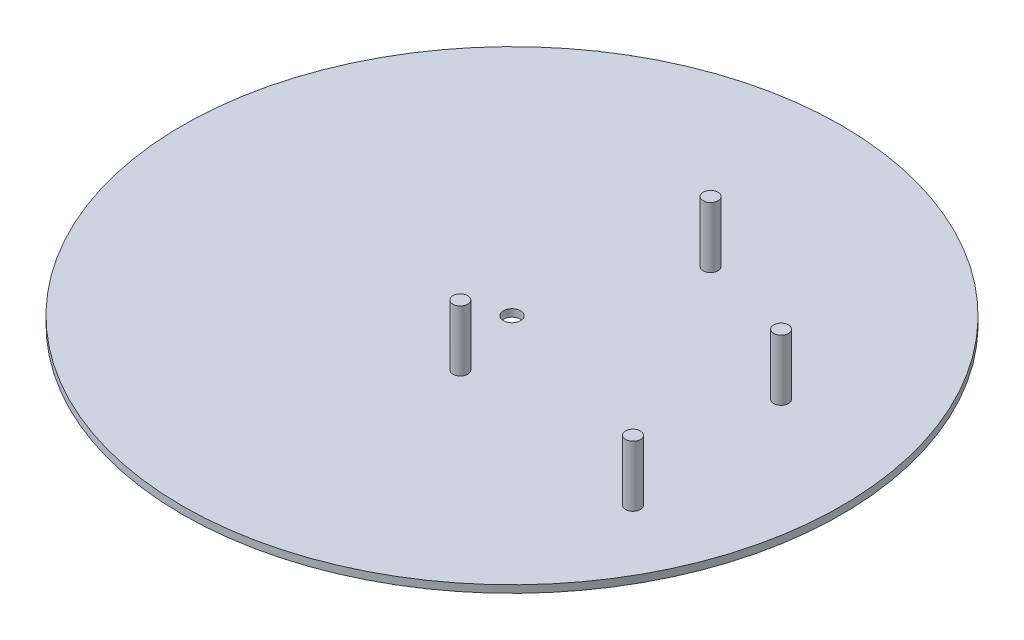
SolidWorks part; units mm, degrees
ref_plane "Front Plane" through (0, 0, 0) normal (0, 0, 1) x (1, 0, 0)
ref_plane "Top Plane" through (0, 0, 0) normal (0, 1, 0) x (1, 0, 0)
ref_plane "Right Plane" through (0, 0, 0) normal (1, 0, 0) x (0, 0, -1)
sketch "Sketch1" plane through (0, 0, 0) normal (0, 1, 0) x (1, 0, 0)
  circle A0 centre (0, 0) radius 111.2642
  circle A1 centre (0, 0) radius 2.92
  circle A4 centre (75.8525, -35) radius 2.5
  circle A6 centre (69.8525, 21) radius 2.5
  circle A8 centre (19.1525, 47.9) radius 2.5
  circle A10 centre (7.1525, -24.6) radius 2.5
  point P4 (0, 0)
  point P5 (0, 0)
  point P14 (0, 0)
  point P15 (0, 0)
  point P16 (0, 0)
extrude "Boss-Extrude12" add sketch "Sketch1" along normal blind 2.5 contours A1 | A4 | A10 | A6 | A8 | A0
sketch "Sketch3" plane through (0, 0, 0) normal (0, -1, 0) x (-1, 0, 0)
  circle A0 centre (-7.1525, -24.6) radius 2.5
sketch "Sketch5" plane through (0, 0, 0) normal (0, -1, 0) x (-1, 0, 0)
  circle A0 centre (-19.1525, 47.9) radius 2.5
extrude "Boss-Extrude15" add sketch "Sketch5" against normal blind 23
sketch "Sketch6" plane through (0, 0, 0) normal (0, -1, 0) x (-1, 0, 0)
  circle A0 centre (-69.8525, 21) radius 2.5
extrude "Boss-Extrude16" add sketch "Sketch6" against normal blind 23
sketch "Sketch7" plane through (0, 0, 0) normal (0, -1, 0) x (-1, 0, 0)
  circle A0 centre (-75.8525, -35) radius 2.5
extrude "Boss-Extrude17" add sketch "Sketch7" against normal blind 23
extrude "Boss-Extrude18" add sketch "Sketch3" against normal blind 23 contours A0
